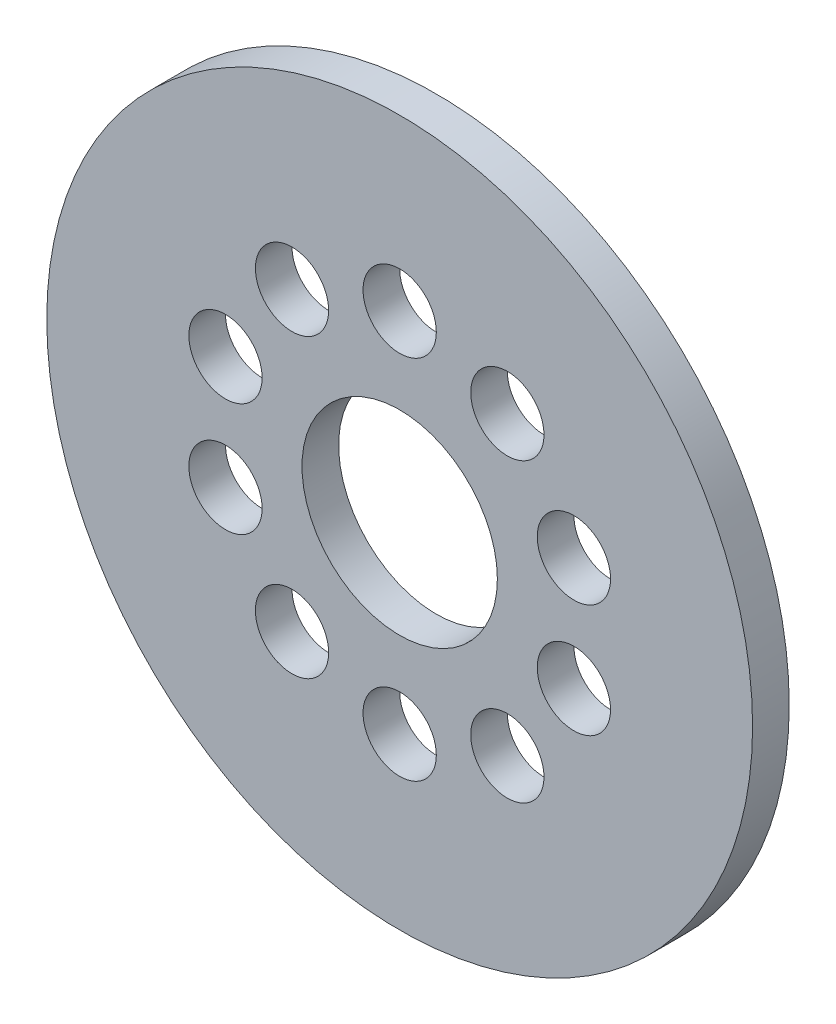
SolidWorks part; units mm, degrees
ref_plane "Front Plane" through (0, 0, 0) normal (0, 0, 1) x (1, 0, 0)
ref_plane "Top Plane" through (0, 0, 0) normal (0, 1, 0) x (1, 0, 0)
ref_plane "Right Plane" through (0, 0, 0) normal (1, 0, 0) x (0, 0, -1)
sketch "Sketch2" plane through (0, 0, 0) normal (0, 0, 1) x (1, 0, 0)
  circle A0 centre (0, 0) radius 144.505
  dimension "D1" = 289.01
extrude "Boss-Extrude1" add sketch "Sketch2" along normal mid plane 15
sketch "Sketch3" plane through (0, 0, 7.5) normal (0, 0, 1) x (1, 0, 0)
  circle A0 centre (0, 0) radius 40
  circle A1 centre (0, 0) radius 75 construction
  circle A2 centre (0, 75) radius 15
  circle A3 centre (44.0839, 60.6763) radius 15
  circle A4 centre (71.3292, 23.1763) radius 15
  circle A5 centre (71.3292, -23.1763) radius 15
  circle A6 centre (44.0839, -60.6763) radius 15
  circle A7 centre (0, -75) radius 15
  circle A8 centre (-44.0839, -60.6763) radius 15
  circle A9 centre (-71.3292, -23.1763) radius 15
  circle A10 centre (-71.3292, 23.1763) radius 15
  circle A11 centre (-44.0839, 60.6763) radius 15
  point P26 (0, 0)
  dimension "D1" = 80
  dimension "D2" = 150
  dimension "D3" = 30
  dimension "D4" = 10
extrude "Cut-Extrude1" cut sketch "Sketch3" against normal through all
